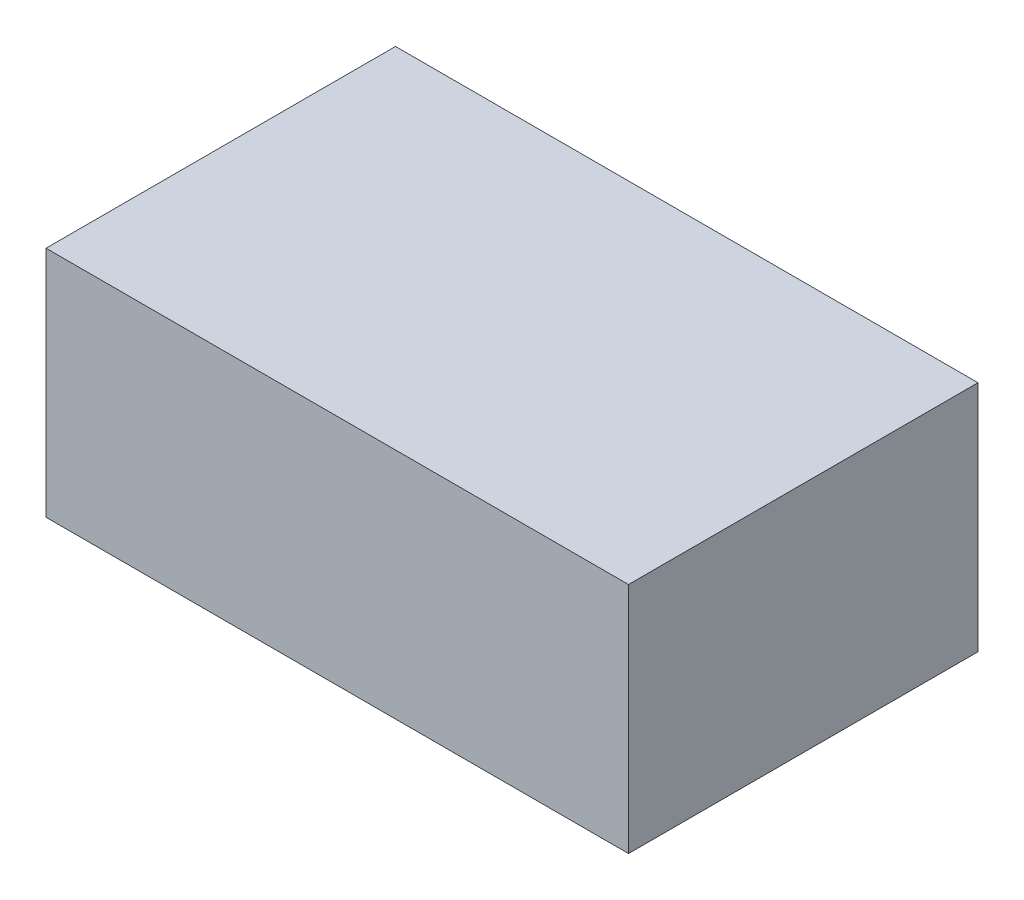
SolidWorks part; units mm, degrees
ref_plane "Front Plane" through (0, 0, 0) normal (0, 0, 1) x (1, 0, 0)
ref_plane "Top Plane" through (0, 0, 0) normal (0, 1, 0) x (1, 0, 0)
ref_plane "Right Plane" through (0, 0, 0) normal (1, 0, 0) x (0, 0, -1)
sketch "Sketch1" plane through (0, 0, 0) normal (0, 1, 0) x (1, 0, 0)
  line L0 (198.8473, 447.546) -> (994.2367, 447.546) construction
  line L1 (8.7796, 5.6678) -> (12.6926, 11.2147)
  line L2 (3.2835, 2.0398) -> (3.2835, 1.9641)
  line L4 (12.6926, 11.2147) -> (14.943, 14.4049)
  line L5 (3.2835, 14.4049) -> (28.2835, 14.4049)
  line L6 (3.2835, 14.4049) -> (3.2835, -0.5951)
  line L7 (3.2835, -0.5951) -> (28.2835, -0.5951)
  line L8 (28.2835, 14.4049) -> (28.2835, -0.5951)
  line L9 (9.4282, 5.2103) -> (13.3412, 10.7572)
  line L10 (13.3412, 10.7572) -> (15.5916, 13.9473)
  line L11 (15.5916, 13.9473) -> (15.9389, 14.4049)
  line L12 (15.9389, 14.4049) -> (14.943, 14.4049)
  line L13 (3.4565, 1.2286) -> (3.2835, 1.19)
  line L14 (3.2835, 1.19) -> (3.2835, 2.0033)
  arc A0 (3.2835, 2.0033) -> (8.7796, 5.6678) centre (1.2845, 10.9551) ccw
  arc A1 (3.4565, 1.2286) -> (9.4282, 5.2103) centre (1.2845, 10.9551) ccw
  dimension "D1" = 15
  dimension "D2" = 25
  dimension "D3" = 0.7937
sketch "Sketch3" plane through (0, 0, 0) normal (0, 1, 0) x (1, 0, 0)
  line L0 (3.2835, 14.4049) -> (28.2835, 14.4049) construction
  line L1 (3.2835, 14.4049) -> (3.2835, -0.5951) construction
  line L2 (3.2835, -0.5951) -> (28.2835, -0.5951) construction
  line L3 (28.2835, 14.4049) -> (28.2835, -0.5951) construction
  line L4 (3.2835, 14.4049) -> (28.2835, 14.4049)
  line L5 (3.2835, 14.4049) -> (3.2835, -0.5951)
  line L6 (3.2835, -0.5951) -> (28.2835, -0.5951)
  line L7 (28.2835, 14.4049) -> (28.2835, -0.5951)
extrude "Boss-Extrude1" add sketch "Sketch3" along normal blind 10
sketch "Sketch4" plane through (0, 0, 0) normal (0, -1, 0) x (1, 0, 0)
  line L0 (9.4282, -5.2103) -> (13.3412, -10.7572) construction
  line L1 (13.3412, -10.7572) -> (15.5916, -13.9473) construction
  line L2 (15.5916, -13.9473) -> (15.9389, -14.4049) construction
  line L3 (12.6926, -11.2147) -> (14.943, -14.4049) construction
  line L4 (8.7796, -5.6678) -> (12.6926, -11.2147) construction
  line L5 (9.4282, -5.2103) -> (13.3412, -10.7572)
  line L6 (13.3412, -10.7572) -> (15.5916, -13.9473)
  line L7 (15.5916, -13.9473) -> (15.9389, -14.4049)
  line L8 (12.6926, -11.2147) -> (14.943, -14.4049)
  line L9 (8.7796, -5.6678) -> (12.6926, -11.2147)
  line L10 (3.4565, -1.2286) -> (3.2835, -1.19) construction
  line L11 (3.4565, -1.2286) -> (3.2835, -1.19)
  line L12 (14.943, -14.4049) -> (15.9389, -14.4049)
  line L13 (3.2835, -1.19) -> (3.2835, -2.0033)
  arc A0 (9.4282, -5.2103) -> (3.4565, -1.2286) centre (1.2845, -10.9551) ccw construction
  arc A1 (8.7796, -5.6678) -> (3.2835, -2.0033) centre (1.2845, -10.9551) ccw construction
  arc A2 (9.4282, -5.2103) -> (3.4565, -1.2286) centre (1.2845, -10.9551) ccw
  arc A3 (8.7796, -5.6678) -> (3.2835, -2.0033) centre (1.2845, -10.9551) ccw
extrude "Cut-Extrude1" cut sketch "Sketch4" against normal blind 2
